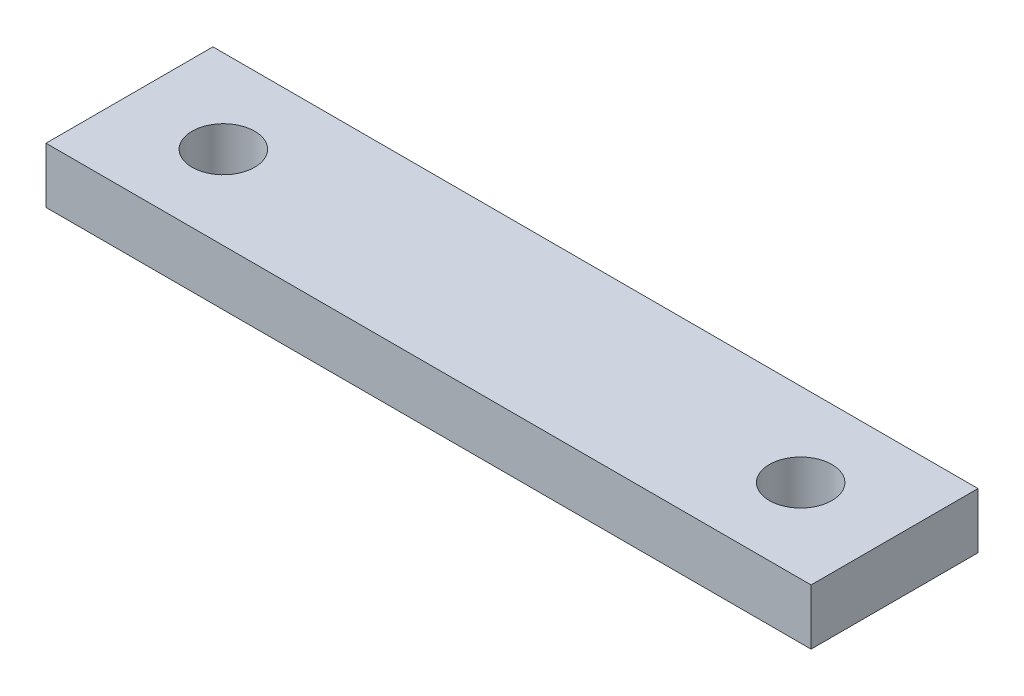
SolidWorks part; units mm, degrees
ref_plane "前视基准面" through (0, 0, 0) normal (0, 0, 1) x (1, 0, 0)
ref_plane "上视基准面" through (0, 0, 0) normal (0, 1, 0) x (1, 0, 0)
ref_plane "右视基准面" through (0, 0, 0) normal (1, 0, 0) x (0, 0, -1)
sketch "草图1" plane through (0, 0, 0) normal (0, 1, 0) x (1, 0, 0)
  line L0 (0, 6) -> (0, -6) construction
  line L1 (27.5, -6) -> (-27.5, -6)
  line L2 (27.5, -6) -> (27.5, 6)
  line L3 (27.5, 6) -> (-27.5, 6)
  line L4 (-27.5, -6) -> (-27.5, 6)
  line L5 (27.5, -6) -> (-27.5, 6) construction
  line L6 (27.5, 6) -> (-27.5, -6) construction
  circle A0 centre (-20.75, 0) radius 2.25
  circle A1 centre (20.75, 0) radius 2.25
  point P0 (0, 0)
  dimension "D3" = 6
  dimension "D1" = 55
  dimension "D2" = 12
  dimension "D4" = 6.75
extrude "凸台-拉伸1" add sketch "草图1" along normal blind 4
